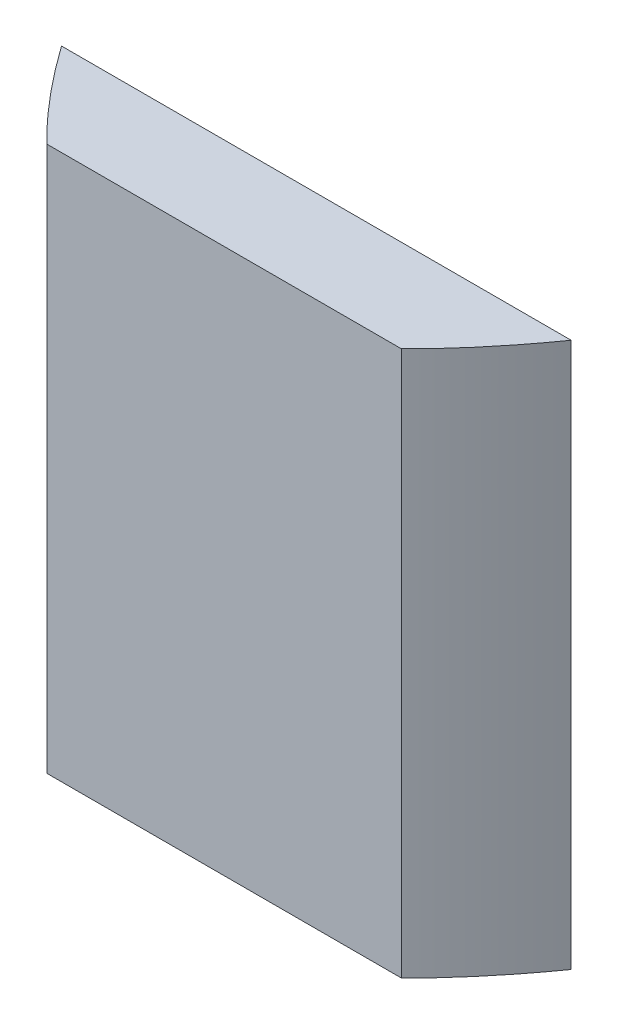
SolidWorks part; units mm, degrees
material "Custom Plastic (2)"
ref_plane "Front Plane" through (0, 0, 0) normal (0, 0, 1) x (1, 0, 0)
ref_plane "Top Plane" through (0, 0, 0) normal (0, 1, 0) x (1, 0, 0)
ref_plane "Right Plane" through (0, 0, 0) normal (1, 0, 0) x (0, 0, -1)
sketch "Sketch1" plane through (0, 0, 0) normal (0, 1, 0) x (1, 0, 0)
  line L0 (-200, 0) -> (200, 0)
  spline S0 degree 2 poles (-225.2396, 53.6645) (0, -453.6645) (225.2396, 53.6645) knots 0 0 0 1 1 1 construction
  spline S1 degree 2 poles (-200, 0) (0, -400) (200, 0) knots 0.056028 0.056028 0.056028 0.943972 0.943972 0.943972
extrude "Boss-Extrude1" add sketch "Sketch1" along normal blind 300
sketch "Sketch2" plane through (0, 300, 0) normal (0, 1, 0) x (1, 0, 0)
  line L0 (200, 0) -> (-200, 0) construction
  line L1 (-242.0011, 78.9581) -> (276.1608, 78.9581)
  line L2 (-242.0011, 78.9581) -> (-242.0011, -101.6)
  line L3 (-242.0011, -101.6) -> (276.1608, -101.6)
  line L4 (276.1608, 78.9581) -> (276.1608, -101.6)
  dimension "D1" = 101.6
extrude "Cut-Extrude1" cut sketch "Sketch2" against normal blind 350
sketch "Sketch3" plane through (0, 300, 0) normal (0, 1, 0) x (1, 0, 0)
  line L0 (-140.2854, -101.6) -> (140.2854, -101.6) construction
  line L1 (-234.4594, -152.4) -> (266.4009, -152.4)
  line L2 (-234.4594, -152.4) -> (-234.4594, -269.0752)
  line L3 (-234.4594, -269.0752) -> (266.4009, -269.0752)
  line L4 (266.4009, -152.4) -> (266.4009, -269.0752)
  dimension "D1" = 50.8
extrude "Cut-Extrude2" cut sketch "Sketch3" against normal blind 350
